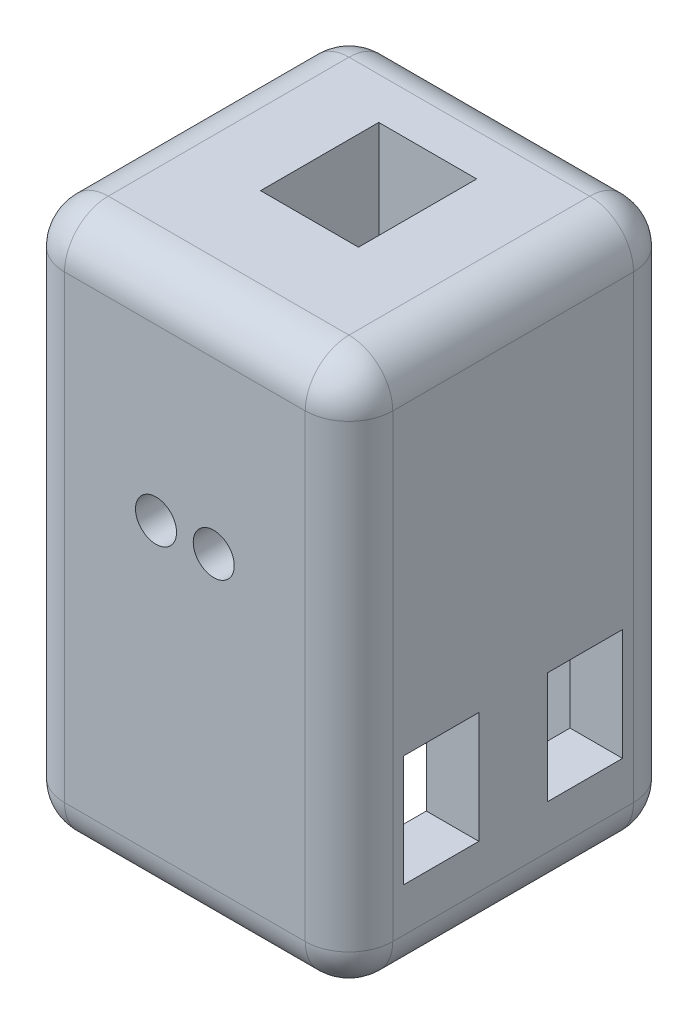
SolidWorks part; units mm, degrees
ref_plane "Front Plane" through (0, 0, 0) normal (0, 0, 1) x (1, 0, 0)
ref_plane "Top Plane" through (0, 0, 0) normal (0, 1, 0) x (1, 0, 0)
ref_plane "Right Plane" through (0, 0, 0) normal (1, 0, 0) x (0, 0, -1)
sketch "Sketch1" plane through (0, 0, 0) normal (0, 1, 0) x (1, 0, 0)
  line L1 (-19.05, -19.05) -> (19.05, -19.05)
  line L2 (-19.05, -19.05) -> (-19.05, 19.05)
  line L3 (-19.05, 19.05) -> (19.05, 19.05)
  line L4 (19.05, -19.05) -> (19.05, 19.05)
  line L5 (0, 19.05) -> (0, -19.05) construction
  line L6 (-19.05, 0) -> (19.05, 0) construction
  point P0 (0, 0)
  dimension "D1" = 38.1
  dimension "D2" = 38.1
extrude "Boss-Extrude1" add sketch "Sketch1" along normal blind 63.5
sketch "Sketch4" plane through (0, 0, 0) normal (1, 0, 0) x (0, 0, -1)
  line L0 (19.05, 63.5) -> (-19.05, 63.5) construction
  line L1 (-4.4577, 215.9) -> (4.4577, 215.9)
  line L2 (-4.4577, 215.9) -> (-4.4577, 63.5)
  line L3 (-4.4577, 63.5) -> (4.4577, 63.5)
  line L4 (4.4577, 215.9) -> (4.4577, 63.5)
  line L5 (0, 63.5) -> (0, 215.9) construction
  line L6 (-4.4577, 139.7) -> (4.4577, 139.7) construction
  point P0 (1.2135, 139.7)
  dimension "D1" = 152.4
  dimension "D2" = 8.9154
extrude "Boss-Extrude3" add sketch "Sketch4" along normal mid plane 11.1125
sketch "Sketch5" plane through (-5.5562, 0, 0) normal (-1, 0, 0) x (0, 0, 1)
  line L0 (-4.4577, 215.9) -> (-8.9586, 214.2617)
  line L1 (-8.9586, 214.2617) -> (-8.9586, 212.5751)
  line L2 (-8.9586, 212.5751) -> (-4.4577, 210.9368)
  line L3 (-4.4577, 63.5) -> (-4.4577, 215.9) construction
  line L4 (-4.4577, 215.9) -> (-4.4577, 210.9368)
  dimension "D1" = 1.6866
  dimension "D2" = 1.6383
  dimension "D3" = 4.5009
extrude "Boss-Extrude4" add sketch "Sketch5" against normal up to surface (11.1125 mm away) up to face at (5.5562, 139.7, 0)
pattern_linear "LPattern1" count 24 spacing 6.2332 along (0, -1, 0) of "Boss-Extrude4"
fillet "Fillet1" radius 0.5004 47 edges at (0, 154.8384, -4.4577) (0, 156.4767, -8.9586) (0, 158.1633, -8.9586) (0, 159.8016, -4.4577) (0, 161.0716, -4.4577) (0, 162.7099, -8.9586) (0, 164.3964, -8.9586) (0, 166.0347, -4.4577) (0, 167.3047, -4.4577) (0, 168.943, -8.9586) (0, 170.6296, -8.9586) (0, 172.2679, -4.4577) (0, 173.5379, -4.4577) (0, 175.1762, -8.9586) (0, 176.8627, -8.9586) (0, 178.501, -4.4577) (0, 179.771, -4.4577) (0, 181.4093, -8.9586) (0, 183.0959, -8.9586) (0, 184.7342, -4.4577) (0, 186.0042, -4.4577) (0, 187.6425, -8.9586) (0, 189.3291, -8.9586) (0, 190.9674, -4.4577) (0, 192.2374, -4.4577) (0, 193.8757, -8.9586) (0, 195.5622, -8.9586) (0, 197.2005, -4.4577) (0, 198.4705, -4.4577) (0, 200.1088, -8.9586) (0, 201.7954, -8.9586) (0, 203.4337, -4.4577) (0, 204.7037, -4.4577) (0, 206.342, -8.9586) (0, 208.0285, -8.9586) (0, 209.6668, -4.4577) (0, 210.9368, -4.4577) (0, 212.5751, -8.9586) (0, 214.2617, -8.9586) (0, 142.3721, -4.4577) (0, 144.0104, -8.9586) (0, 145.6969, -8.9586) (0, 147.3352, -4.4577) (0, 148.6052, -4.4577) (0, 150.2435, -8.9586) (0, 151.9301, -8.9586) (0, 153.5684, -4.4577)
sketch "Sketch8" plane through (0, 0, 0) normal (0, -1, 0) x (1, 0, 0)
  line L1 (12.954, -12.954) -> (-12.954, -12.954)
  line L2 (12.954, -12.954) -> (12.954, 12.954)
  line L3 (12.954, 12.954) -> (-12.954, 12.954)
  line L4 (-12.954, -12.954) -> (-12.954, 12.954)
  line L5 (0, 12.954) -> (0, -12.954) construction
  line L6 (12.954, 0) -> (-12.954, 0) construction
  point P0 (0, 0)
  dimension "D1" = 25.908
extrude "Cut-Extrude3" cut sketch "Sketch8" against normal offset from surface (35.56 mm away) 27.94 up to face at (0, 63.5, 0)
sketch "Sketch9" plane through (0, 35.56, 0) normal (0, -1, 0) x (1, 0, 0)
  line L1 (-6.35, -6.35) -> (6.35, -6.35)
  line L2 (-6.35, -6.35) -> (-6.35, 6.35)
  line L3 (-6.35, 6.35) -> (6.35, 6.35)
  line L4 (6.35, -6.35) -> (6.35, 6.35)
  line L5 (0, 6.35) -> (0, -6.35) construction
  line L6 (-6.35, 0) -> (6.35, 0) construction
  point P0 (0, 0)
  dimension "D1" = 12.7
  dimension "D2" = 12.7
extrude "Cut-Extrude4" cut sketch "Sketch9" against normal blind 6.35
sketch "Sketch10" plane through (0, 0, 6.35) normal (0, 0, -1) x (-1, 0, 0)
  line L0 (-6.35, 41.91) -> (-6.35, 35.56) construction
  line L1 (6.35, 41.91) -> (6.35, 35.56) construction
  line L2 (-6.35, 41.91) -> (6.35, 41.91) construction
  circle A0 centre (-3.35, 38.735) radius 2.3812
  circle A1 centre (3.35, 38.735) radius 2.3812
  point P6 (-6.35, 38.735)
  point P9 (6.35, 38.735)
  dimension "D1" = 4.7625
  dimension "D2" = 3
  dimension "D3" = 3
  dimension "D4" = 3.175
extrude "Cut-Extrude5" cut sketch "Sketch10" against normal through all both and the other way through all
sketch "Sketch11" plane through (-19.05, 0, 0) normal (-1, 0, 0) x (0, 0, 1)
  line L0 (0, 63.5) -> (0, 0) construction
  line L1 (-12.7, 23.114) -> (-3.9793, 23.114)
  line L2 (-12.7, 23.114) -> (-12.7, 10.16)
  line L3 (-12.7, 10.16) -> (-3.9793, 10.16)
  line L4 (-3.9793, 23.114) -> (-3.9793, 10.16)
  line L5 (-8.3397, 10.16) -> (-8.3397, 23.114) construction
  line L6 (-12.7, 16.637) -> (-3.9793, 16.637) construction
  line L7 (-19.05, 63.5) -> (19.05, 63.5) construction
  line L8 (12.7, 16.637) -> (3.9793, 16.637) construction
  line L9 (8.3397, 10.16) -> (8.3397, 23.114) construction
  line L10 (3.9793, 23.114) -> (3.9793, 10.16)
  line L11 (12.7, 10.16) -> (3.9793, 10.16)
  line L12 (12.7, 23.114) -> (12.7, 10.16)
  line L13 (12.7, 23.114) -> (3.9793, 23.114)
  line L15 (-19.05, 63.5) -> (-19.05, 0) construction
  point P0 (-8.3397, 16.637)
  point P16 (8.3397, 16.637)
  dimension "D1" = 8.7207
  dimension "D2" = 53.34
  dimension "D3" = 12.954
  dimension "D4" = 6.35
extrude "Cut-Extrude6" cut sketch "Sketch11" against normal through all
fillet "Fillet2" radius 0.635 4 edges at (5.7312, 38.735, 6.35) (-0.9688, 38.735, 6.35) (0.9688, 38.735, -6.35) (-5.7312, 38.735, -6.35)
fillet "Fillet3" radius 5.08 12 edges at (-19.05, 0, 0) (0, 0, 19.05) (0, 0, -19.05) (19.05, 0, 0) (19.05, 31.75, 19.05) (19.05, 31.75, -19.05) (19.05, 63.5, 0) (0, 63.5, -19.05) (0, 63.5, 19.05) (-19.05, 31.75, 19.05) (-19.05, 31.75, -19.05) (-19.05, 63.5, 0)
sketch "Sketch13" plane through (0, 63.5, 0) normal (0, 1, 0) x (1, 0, 0)
  line L0 (-5.5562, 8.9586) -> (5.5562, 8.9586) construction
  line L1 (19.05, 19.05) -> (-19.05, 19.05)
  line L2 (19.05, 19.05) -> (19.05, -19.05)
  line L3 (19.05, -19.05) -> (-19.05, -19.05)
  line L4 (-19.05, 19.05) -> (-19.05, -19.05)
  line L5 (0, -19.05) -> (0, 19.05) construction
  line L6 (19.05, 0) -> (-19.05, 0) construction
  line L7 (5.5562, -4.4577) -> (-5.5562, -4.4577)
  line L8 (5.5562, -4.4577) -> (5.5562, 8.9586)
  line L9 (5.5562, 8.9586) -> (-5.5562, 8.9586)
  line L10 (-5.5562, -4.4577) -> (-5.5562, 8.9586)
  line L11 (0, 8.9586) -> (0, -4.4577) construction
  line L12 (5.5562, 2.2504) -> (-5.5562, 2.2504) construction
  line L13 (-5.5562, -4.4577) -> (-5.5562, 4.4577) construction
  point P0 (0, 0)
  point P168 (0, 2.2504)
  dimension "D1" = 38.1
extrude "Cut-Extrude7" [suppressed] cut sketch "Sketch13" against normal through all
sketch "Sketch14" [suppressed] plane through (0, 0, -6.35) normal (0, 0, 1) x (1, 0, 0)
  line L1 (-5.5562, 41.91) -> (5.5563, 41.91)
  line L2 (-5.5562, 41.91) -> (-5.5562, 35.56)
  line L3 (-5.5562, 35.56) -> (5.5563, 35.56)
  line L4 (5.5563, 41.91) -> (5.5563, 35.56)
  line L5 (0, 35.56) -> (0, 41.91) construction
  line L6 (-5.5562, 38.735) -> (5.5563, 38.735) construction
  point P160 (0, 38.735)
extrude "Cut-Extrude8" [suppressed] cut sketch "Sketch14" against normal through all
sketch "Sketch15" plane through (0, 215.9, 0) normal (0, 1, 0) x (1, 0, 0)
  line L1 (5.5562, -4.4577) -> (5.5562, 4.4577) construction
  line L2 (-5.6832, 9.1374) -> (5.6832, 9.1374)
  line L3 (-5.6832, 9.1374) -> (-5.6832, -4.5847)
  line L4 (-5.6832, -4.5847) -> (5.6832, -4.5847)
  line L5 (5.6832, 9.1374) -> (5.6832, -4.5847)
  line L6 (0, -4.5847) -> (0, 9.1374) construction
  line L9 (-5.6832, 2.2763) -> (5.6832, 2.2763) construction
  line L10 (-5.5562, -4.4577) -> (-5.5562, 4.4577) construction
  line L11 (5.5562, -4.4577) -> (-5.5562, -4.4577) construction
  line L12 (5.5562, 8.6294) -> (-5.5562, 8.6294) construction
  point P0 (0, 2.2763)
  dimension "D1" = 0.127
  dimension "D2" = 0.127
  dimension "D3" = 0.127
  dimension "D4" = 0.508
extrude "Cut-Extrude9" cut sketch "Sketch15" against normal up to surface (173.99 mm away) up to face at (0, 41.91, 0)
